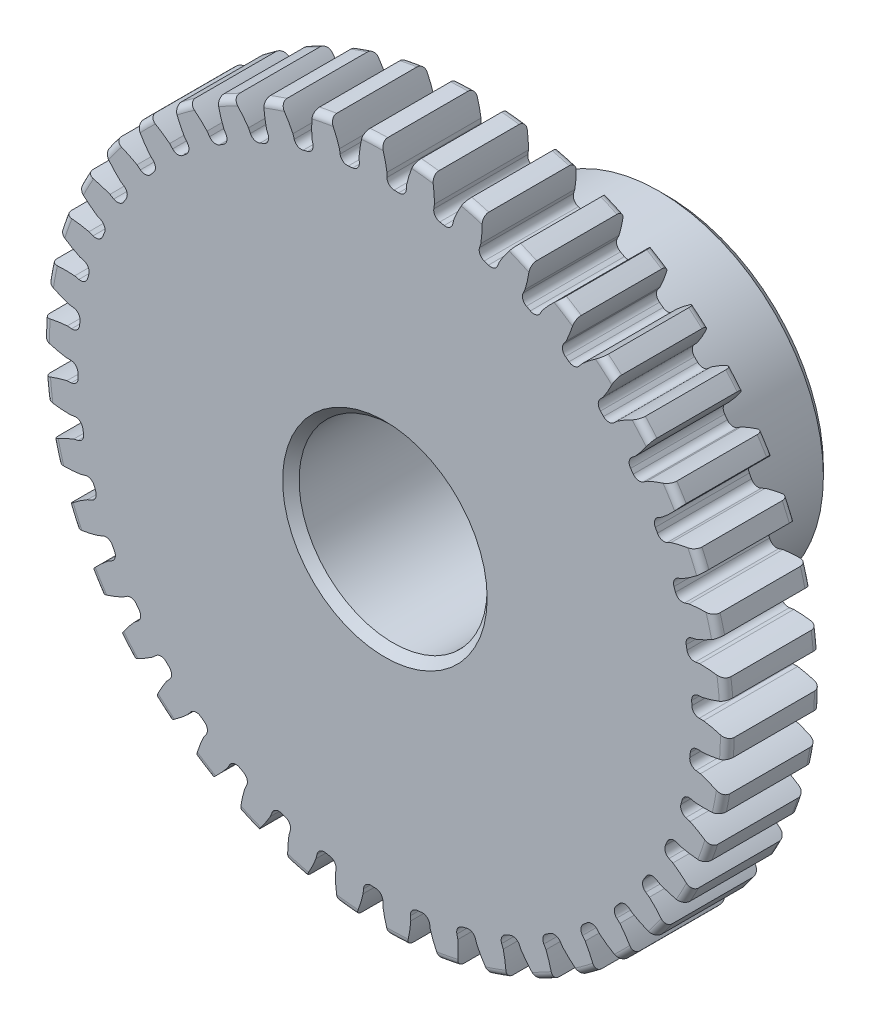
SolidWorks part; units mm, degrees
ref_plane "Front" through (0, 0, 0) normal (0, 0, 1) x (1, 0, 0)
ref_plane "Top" through (0, 0, 0) normal (0, 1, 0) x (1, 0, 0)
ref_plane "Right" through (0, 0, 0) normal (1, 0, 0) x (0, 0, -1)
sketch "Sketch1" plane through (0, 0, 0) normal (0, 0, 1) x (1, 0, 0)
  line L0 (-533.4, 0) -> (533.4, 0) construction
  circle A0 centre (0, 0) radius 11.557
  circle A1 centre (0, 0) radius 11.1125 construction
  circle A3 centre (0, 0) radius 10.3664 construction
  dimension "D1" = 1.1906
  dimension "OD" = 23.114
  dimension "Ptich Dia" = 22.225
  dimension "Root Dia" = 20.7327
  dimension "D3" = 0.4445
  dimension "Number of Teeth" = 1066.8
extrude "Boss-Extrude1" add sketch "Sketch1" against normal blind 3.175
sketch "Sketch2" plane through (0, 0, 0) normal (1, 0, 0) x (0, 0, -1)
  line L0 (3.175, 0) -> (9.525, 0)
  line L1 (3.175, 0) -> (3.175, 5.5562)
  line L2 (3.175, 5.5562) -> (9.525, 5.5562)
  line L3 (9.525, 5.5562) -> (9.525, 0)
  point P5 (9.525, -5.5562)
  point P6 (0, -11.557)
  point P7 (3.175, -11.557)
  point P9 (0, 11.557)
  dimension "Face Wd" = 3.175
  dimension "B Hub Dia" = 11.1125
  dimension "D O'all Lg." = 9.525
revolve "Revolve1" add sketch "Sketch2" angle 360 about L0
fillet "Fillet2" radius 0.2311 3 edges at (11.557, 0, -3.175) (11.557, 0, 0) (5.5562, 0, -3.175)
sketch "Sketch3" plane through (0, 0, 0) normal (0, 0, 1) x (1, 0, 0)
  line L0 (0, 0) -> (0, 11.557) construction
  line L1 (-2.6937, 10.4159) -> (0, 11.1125)
  line L2 (-9.5921, 11.1125) -> (9.5921, 11.1125) construction
  line L3 (-9.2865, 8.7108) -> (9.2865, 13.5142) construction
  line L4 (-2.6937, 10.4159) -> (0, 0) construction
  line L5 (-6.8708, 8.2788) -> (0, 0) construction
  line L6 (-6.8708, 8.2788) -> (-1.1095, 13.0602) construction
  line L7 (-1.8783, 10.5933) -> (0, 0) construction
  line L8 (-1.8783, 10.5933) -> (0.0394, 10.9333) construction
  arc A0 (-2.6937, 10.4159) -> (-6.8708, 8.2788) centre (0, 0) ccw
  circle A1 centre (0, 0) radius 11.1125 construction
  circle A2 centre (0, 0) radius 10.7585 construction
  arc A3 (-2.6937, 10.4159) -> (-1.8783, 10.5933) centre (0, 0) cw
  circle A4 centre (0, 0) radius 11.557 construction
  point P6 (0, 11.1125)
  dimension "D1" = 2.7823
  dimension "Pressure Angle" = 14.5
  dimension "D2" = 4.73
  dimension "D3" = 7.4869
  dimension "D4" = 0.8347
  dimension "D5" = 1.9476
sketch "Sketch4" plane through (0, 0, 0) normal (0, 0, 1) x (1, 0, 0)
  line L0 (0, 0) -> (0.4152, 11.097) construction
  line L1 (0.0698, 10.7583) -> (0.0698, 10.3661)
  line L2 (0, 11.1125) -> (0.8304, 11.0814) construction
  line L3 (0.7344, 10.7334) -> (0.7051, 10.3424)
  line L4 (0.0698, 10.3661) -> (0, 0) construction
  line L5 (0, 0) -> (0, 11.557) construction
  line L6 (-6.8708, 8.2788) -> (-1.1095, 13.0602) construction
  line L7 (-6.8708, 8.2788) -> (-1.1095, 13.0602) construction
  arc A0 (0.7051, 10.3424) -> (0.0698, 10.3661) centre (0, 0) ccw
  arc A1 (0, 11.1125) -> (0.8304, 11.0814) centre (0, 0) cw construction
  circle A2 centre (0, 0) radius 11.1125 construction
  circle A3 centre (0, 0) radius 10.7585 construction
  circle A4 centre (0, 0) radius 10.3664 construction
  arc A5 (2.0824, 12.9408) -> (-1.1095, 13.0602) centre (0, 0) ccw
  spline S0 degree 2 poles (-1.1095, 13.0602) (-0.1251, 12.0461) (0.0698, 10.7583) knots 0 0 0 1 1 1
  spline S1 degree 2 poles (2.0824, 12.9408) (1.025, 12.003) (0.7344, 10.7334) knots 0 0 0 1 1 1
  dimension "D1" = 0.8312
extrude "Cut-Extrude1" cut sketch "Sketch4" against normal through all
fillet "Fillet1" radius 0.2494 2 edges at (0.7051, 10.3424, -1.5875) (0.0698, 10.3661, -1.5875)
pattern_circular "CirPattern1" count 42 over 360 about axis through (0, 0, -3.175) along (0, 0, 1) of "Cut-Extrude1", "Fillet1"
sketch "Sketch5" plane through (0, 0, 0) normal (0, 0, 1) x (1, 0, 0)
  circle A0 centre (0, 0) radius 3.175
  circle A1 centre (0, 0) radius 1.5875 construction
  dimension "Bore Min" = 6.35
  dimension "Bore Max" = 3.175
extrude "Cut-Extrude2" cut sketch "Sketch5" against normal through all
chamfer "Chamfer1" distance 0.2778 angle 45 3 edges at (5.5562, 0, -9.525) (3.175, 0, 0) (3.175, 0, -9.525)
sketch "Pitch Dia" plane through (0, 0, 0) normal (0, 0, 1) x (1, 0, 0)
  circle A0 centre (0, 0) radius 11.1125 construction
  circle A1 centre (0, 0) radius 11.1125 construction
equation "\"D1@Boss-Extrude1\" = \"Face Wd@Sketch2\""
equation "\"D2@Sketch3\" = \"D1@Sketch3\"*1.7"
equation "\"D3@Sketch3\" = \"D1@Sketch3\"+\"D2@Sketch3\"-.001"
equation "\"D4@Sketch3\" = \"D1@Sketch3\"*.3"
equation "\"D5@Sketch3\" = \"D1@Sketch3\"-\"D4@Sketch3\""
equation "\"D1@Sketch4\" = 1.5708/(\"Number of Teeth@Sketch1\"/\"Ptich Dia@Sketch1\")"
equation "\"D1@Chamfer1\" = \"B Hub Dia@Sketch2\"*.025"
equation "\"D1@CirPattern1\" = \"Number of Teeth@Sketch1\""
equation "\"D1@Fillet1\" = \"D1@Sketch4\"*.3"
equation "\"D1@Fillet2\" = \"OD@Sketch1\"*.01"
equation "\"D1@Sketch1\" = 2.250/(\"Number of Teeth@Sketch1\"/\"Ptich Dia@Sketch1\")"
